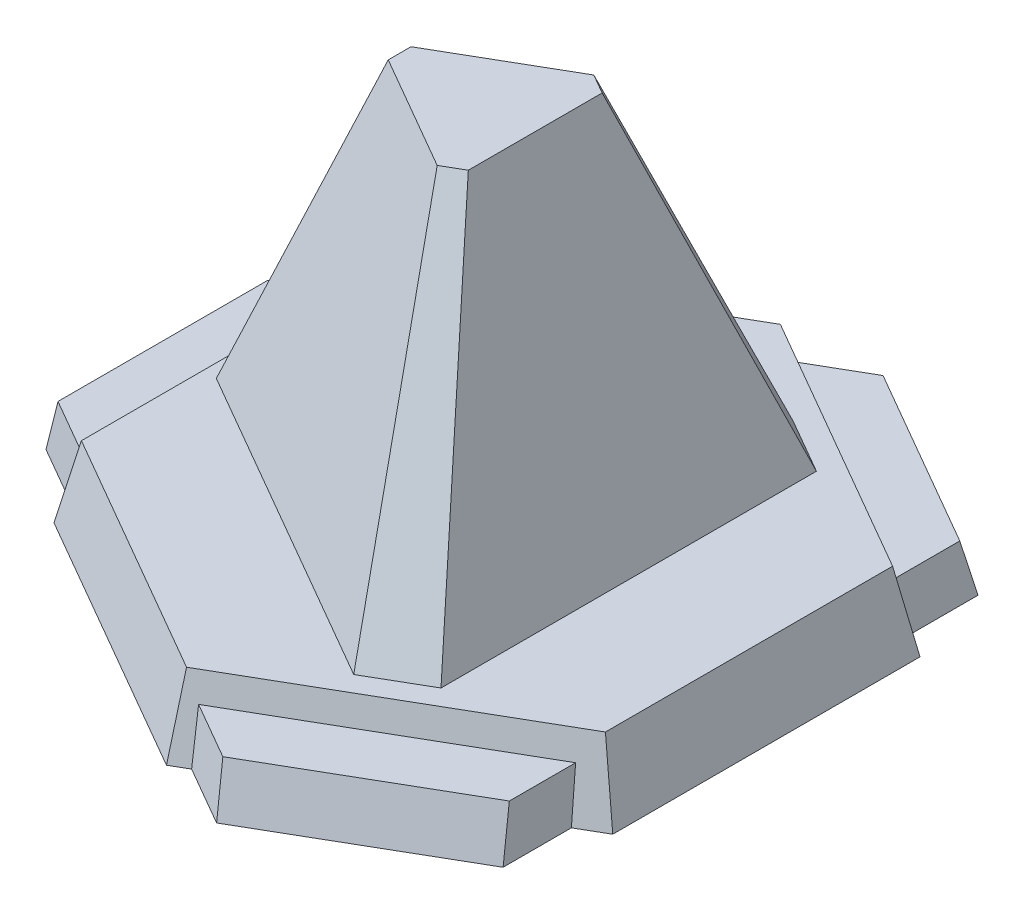
SolidWorks part; units mm, degrees
ref_plane "前视基准面" through (0, 0, 0) normal (0, 0, 1) x (1, 0, 0)
ref_plane "上视基准面" through (0, 0, 0) normal (0, 1, 0) x (1, 0, 0)
ref_plane "右视基准面" through (0, 0, 0) normal (1, 0, 0) x (0, 0, -1)
sketch "草图1" plane through (0, 0, 0) normal (0, 1, 0) x (1, 0, 0)
  line L0 (-225.196, 0) -> (523.4285, 0) construction
  line L1 (0, -454.9568) -> (0, 436.6976) construction
  line L2 (-664.4724, 409.655) -> (-664.4724, -409.655)
  line L3 (-664.4724, -409.655) -> (0, -793.295)
  line L4 (0, -793.295) -> (709.5404, -383.635)
  line L5 (709.5404, -383.635) -> (709.5404, 383.635)
  line L6 (709.5404, 383.635) -> (0, 793.295)
  line L7 (0, 793.295) -> (-664.4724, 409.655)
  line L8 (-710.8824, -436.4496) -> (0, -846.8849)
  line L9 (0, -846.8849) -> (755.9504, -410.4296)
  line L10 (755.9504, -410.4296) -> (755.9504, 410.4296)
  line L11 (755.9504, 410.4296) -> (0, 846.8849)
  line L12 (0, 846.8849) -> (-710.8824, 436.4496)
  line L13 (-710.8824, 436.4496) -> (-710.8824, -436.4496)
  dimension "D1" = 767.27
  dimension "D2" = 819.31
  dimension "D3" = 767.27
  dimension "D4" = 819.31
  dimension "D5" = 819.31
  dimension "D6" = 767.27
  dimension "D7" = 1586.59
  dimension "D8" = 46.41
sketch "草图2" plane through (0, 0, 0) normal (1, 0, 0) x (0, 0, -1)
  line L0 (0, 367.5978) -> (0, -423.4637) construction
  line L1 (0, 0) -> (0, 200)
  dimension "D1" = 200
ref_plane "基准面1" through (0, 200, 0) normal (0, 1, 0) x (1, 0, 0)
sketch "草图4" plane through (0, 200, 0) normal (0, 1, 0) x (1, 0, 0)
  line L0 (0, 793.295) -> (-664.4724, 409.655) construction
  line L1 (709.5404, 383.635) -> (0, 793.295) construction
  line L2 (709.5404, -383.635) -> (709.5404, 383.635) construction
  line L3 (0, -793.295) -> (709.5404, -383.635) construction
  line L4 (-664.4724, -409.655) -> (0, -793.295) construction
  line L5 (-664.4724, 409.655) -> (-664.4724, -409.655) construction
  line L6 (0, 793.295) -> (-664.4724, 409.655)
  line L7 (709.5404, 383.635) -> (0, 793.295)
  line L8 (709.5404, -383.635) -> (709.5404, 383.635)
  line L9 (0, -793.295) -> (709.5404, -383.635)
  line L10 (-664.4724, -409.655) -> (0, -793.295)
  line L11 (-664.4724, 409.655) -> (-664.4724, -409.655)
loft "放样5" add profiles "草图4" section "草图4" section "草图1"
sketch "草图6" plane through (0, 200, 0) normal (0, 1, 0) x (1, 0, 0)
  line L0 (-664.4724, 384.41) -> (-845.0301, 280.165)
  line L1 (-664.4724, 409.655) -> (-664.4724, -409.655) construction
  line L2 (-845.0301, 280.165) -> (-845.0301, -280.165)
  line L3 (-845.0301, -280.165) -> (-664.4724, -384.41)
  line L4 (-664.4724, -384.41) -> (-664.4724, 384.41)
  line L8 (-1681.2594, 0) -> (0, 0) construction
  dimension "D1" = 768.82
  dimension "D2" = 208.49
  dimension "D3" = 208.49
  dimension "D4" = 560.33
sketch "草图7" plane through (0, 0, 0) normal (0, 1, 0) x (1, 0, 0)
  line L0 (-710.8824, 387.2742) -> (-891.4401, 283.0292)
  line L1 (-710.8824, 436.4496) -> (-710.8824, -436.4496) construction
  line L2 (-891.4401, 283.0292) -> (-891.4401, -277.3008)
  line L3 (-891.4401, -277.3008) -> (-710.8824, -381.5458)
  line L4 (-845.0301, -280.165) -> (-664.4724, -384.41) construction
  line L5 (-845.0301, 280.165) -> (-845.0301, -280.165) construction
  line L6 (-664.4724, 384.41) -> (-845.0301, 280.165) construction
  line L9 (-1213.4792, 2.8642) -> (0, 2.8642) construction
  line L10 (-710.8824, -381.5458) -> (-710.8824, 387.2742)
  dimension "D1" = 560.33
  dimension "D2" = 208.49
ref_plane "基准面2" through (0, 130.08, 0) normal (0, 1, 0) x (1, 0, 0)
sketch "草图8" plane through (0, 130.08, 0) normal (0, 1, 0) x (1, 0, 0)
  line L0 (-676.0324, 384.41) -> (-676.0324, -384.41)
  line L1 (-676.0324, -384.41) -> (-856.5901, -280.165)
  line L2 (-856.5901, -280.165) -> (-856.5901, 280.165)
  line L3 (-856.5901, 280.165) -> (-676.0324, 384.41)
  line L4 (-116.2596, 0) -> (207.8033, 0) construction
  dimension "D1" = 208.49
  dimension "D2" = 208.49
  dimension "D3" = 560.33
  dimension "D4" = 768.82
loft "放样8" add profiles "草图8", "草图7"
pattern_circular "阵列(圆周)1" count 3 every 120 about axis through (0, 0, 0) along (0, 1, 0) of "放样8"
sketch "草图10" plane through (0, 200, 0) normal (0, 1, 0) x (1, 0, 0)
  line L0 (0, 0) -> (366.768, 635.2609) construction
  line L1 (4.1123, -7.1227) -> (314.2816, -544.3428) construction
  line L2 (240.3015, 586.8744) -> (388.0974, 501.5444)
  line L3 (670.925, 601.7463) -> (185.665, 881.9113) construction
  line L4 (388.0974, 501.5444) -> (388.0974, -501.5356)
  line L5 (388.0974, -501.5356) -> (240.3021, -586.8666)
  line L6 (240.3021, -586.8666) -> (-628.3906, -85.3266)
  line L7 (-628.3906, -85.3266) -> (-628.3906, 85.3334)
  line L8 (-628.3906, 85.3334) -> (240.3015, 586.8744)
  line L9 (0, -793.295) -> (709.5404, -383.635) construction
  line L10 (-664.4724, 409.655) -> (-664.4724, -409.655) construction
  line L11 (709.5404, -383.635) -> (709.5404, 383.635) construction
  point P20 (428.295, 741.8288)
  dimension "D1" = 170.66
  dimension "D2" = 1003.08
ref_plane "基准面3" through (0, 1111.8, 0) normal (0, 1, 0) x (1, 0, 0)
sketch "草图11" plane through (0, 1111.8, 0) normal (0, 1, 0) x (1, 0, 0)
  line L0 (-223.9849, 30.4163) -> (-223.9849, -30.4139)
  line L1 (-223.9849, -30.4139) -> (85.6539, -209.1839)
  line L2 (85.6539, -209.1839) -> (138.3342, -178.7684)
  line L3 (138.3342, -178.7684) -> (138.3342, 178.7716)
  line L4 (138.3342, 178.7716) -> (85.6536, 209.1867)
  line L5 (85.6536, 209.1867) -> (-223.9849, 30.4163)
  line L6 (-628.3906, 85.3334) -> (240.3015, 586.8744) construction
  line L7 (-628.3906, -85.3266) -> (-628.3906, 85.3334) construction
  line L8 (240.3021, -586.8666) -> (-628.3906, -85.3266) construction
  line L9 (388.0974, -501.5356) -> (240.3021, -586.8666) construction
  line L10 (240.3015, 586.8744) -> (388.0974, 501.5444) construction
  line L11 (91.073, 157.743) -> (-128.201, -222.0507) construction
  line L13 (103.5439, -179.3405) -> (344.0511, -595.9043) construction
  dimension "D1" = 357.54
loft "放样9" add profiles "草图11", "草图10"
